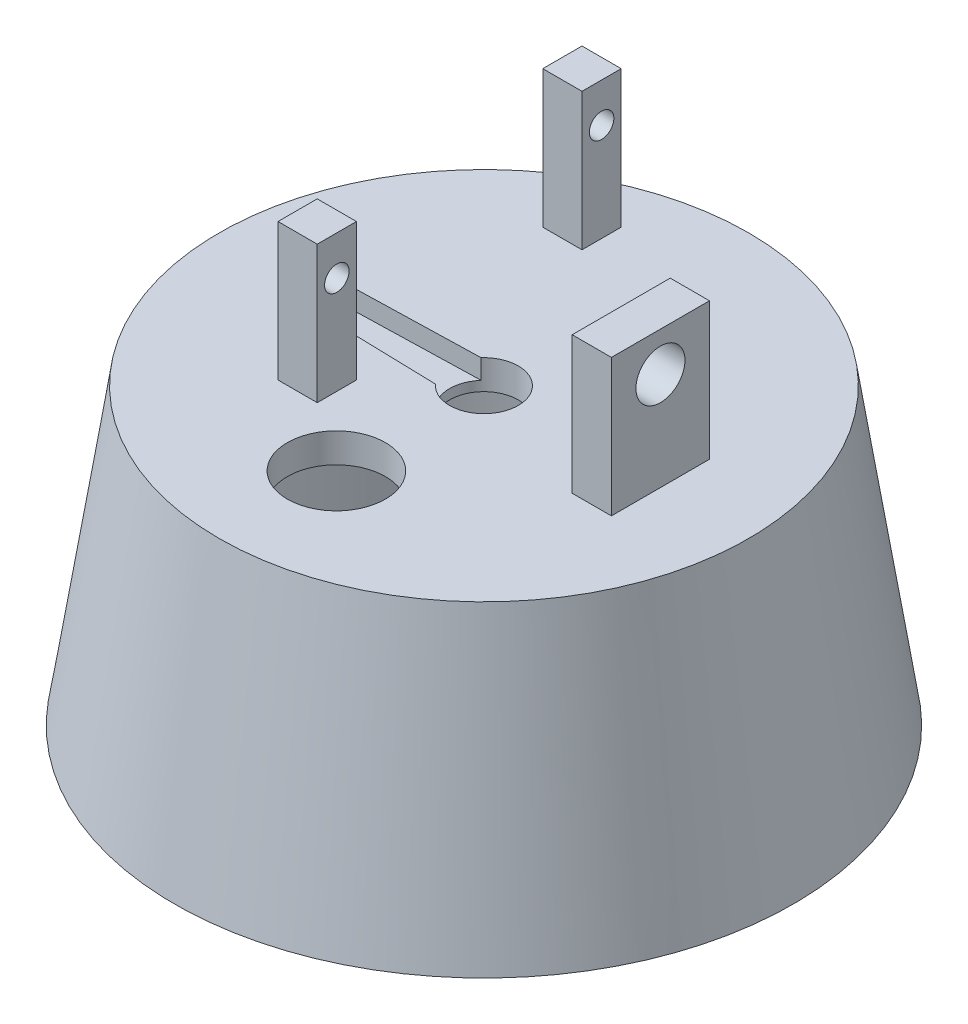
SolidWorks part; units mm, degrees
ref_plane "前视基准面" through (0, 0, 0) normal (0, 0, 1) x (1, 0, 0)
ref_plane "上视基准面" through (0, 0, 0) normal (0, 1, 0) x (1, 0, 0)
ref_plane "右视基准面" through (0, 0, 0) normal (1, 0, 0) x (0, 0, -1)
sketch "草图1" plane through (0, 0, 0) normal (0, 1, 0) x (1, 0, 0)
  circle A0 centre (0, 0) radius 27
  circle A1 centre (0, 0) radius 25.25
  dimension "D1" = 54
  dimension "D2" = 50.5
extrude "凸台-拉伸1" add sketch "草图1" along normal blind 27
sketch "草图3" plane through (0, 27, 0) normal (0, 1, 0) x (1, 0, 0)
  circle A0 centre (0, 0) radius 2.4
  circle A1 centre (0, 0) radius 27 construction
  circle A2 centre (0, 0) radius 27
  dimension "D1" = 4.8
extrude "凸台-拉伸2" add sketch "草图3" along normal blind 3
sketch "草图5" plane through (0, 0, 0) normal (0, 0, 1) x (1, 0, 0)
  line L0 (27, 30) -> (31.564, 0)
  line L1 (31.564, 0) -> (27, 0)
  line L2 (29.7, 0) -> (-29.7, 0) construction
  line L3 (27, 0) -> (27, 30) construction
  line L4 (27, 0) -> (27, 30)
  line L5 (0, 0) -> (0, 32.1264) construction
sketch "草图7" plane through (0, 30, 0) normal (0, 1, 0) x (1, 0, 0)
  line L0 (0, 5.5) -> (-29.1965, 5.5) construction
  line L2 (-7, 21) -> (-11, 21)
  line L3 (-7, 21) -> (-7, 17)
  line L4 (-7, 17) -> (-11, 17)
  line L5 (-11, 21) -> (-11, 17)
  line L6 (-11, -6) -> (-7, -6)
  line L7 (-11, -6) -> (-11, -10)
  line L8 (-11, -10) -> (-7, -10)
  line L9 (-7, -6) -> (-7, -10)
  dimension "D1" = 4
  dimension "D2" = 23
  dimension "D3" = 5.5
  dimension "D4" = 7
  dimension "D5" = 4
  dimension "D6" = 4
revolve "旋转2" add sketch "草图5" angle 360 about L5
extrude "凸台-拉伸3" add sketch "草图7" along normal blind 14
sketch "草图8" plane through (-7, 0, 0) normal (1, 0, 0) x (0, 0, -1)
  line L16 (-6, 40) -> (17, 40) construction
  line L17 (5.5, 40) -> (5.5, 30) construction
  line L18 (27, 30) -> (-27, 30) construction
  circle A0 centre (-8, 40) radius 1.25
  circle A1 centre (19, 40) radius 1.25
  point P0 (0, 0)
  dimension "D1" = 2.5
  dimension "D2" = 10
  dimension "D3" = 27
extrude "切除-拉伸1" cut sketch "草图8" against normal blind 14
sketch "草图10" plane through (0, 30, 0) normal (0, 1, 0) x (1, 0, 0)
  line L0 (0, 0) -> (-8.8896, 0) construction
  line L1 (14, -5) -> (18, -5)
  line L2 (14, -5) -> (14, 5)
  line L3 (14, 5) -> (18, 5)
  line L4 (18, -5) -> (18, 5)
  line L5 (16, 5) -> (16, -5) construction
  line L6 (14, 0) -> (18, 0) construction
  point P0 (16, 0)
  dimension "D1" = 18
  dimension "D2" = 4
  dimension "D3" = 10
extrude "凸台-拉伸4" add sketch "草图10" along normal blind 14
sketch "草图11" plane through (18, 0, 0) normal (1, 0, 0) x (0, 0, -1)
  line L0 (0, 44) -> (0, 30) construction
  line L1 (-5, 44) -> (5, 44) construction
  line L2 (27, 30) -> (-27, 30) construction
  circle A0 centre (-8, 40) radius 1.25 construction
  circle A2 centre (0, 40) radius 2.5
  point P15 (0, 0)
  point P16 (0, 0)
  dimension "D1" = 5
extrude "切除-拉伸3" cut sketch "草图11" against normal blind 14
sketch "草图12" plane through (0, 30, 0) normal (0, 1, 0) x (1, 0, 0)
  circle A0 centre (0, -15.0451) radius 5
extrude "切除-拉伸4" cut sketch "草图12" against normal blind 14
sketch "草图13" plane through (0, 30, 0) normal (0, 1, 0) x (1, 0, 0)
  line L0 (0, 0) -> (-23.4475, 0) construction
  line L1 (-15, 2) -> (-0.0641, 2.3991)
  line L2 (-15.0533, -1.9993) -> (-0.064, -2.3991)
  circle A0 centre (-15, 0) radius 2
  circle A1 centre (0, 0) radius 2.4 construction
  circle A2 centre (0, 0) radius 2.4
  circle A3 centre (0, 0) radius 3.5
  circle M6 centre (0, 0) radius 2.4
  dimension "D2" = 4
  dimension "D3" = 7
  dimension "D1" = 15
extrude "切除-拉伸5" cut sketch "草图13" against normal blind 2 contours L0 A3 L1 A0 | A3 L0 A0 L2 | L0 A2 L1 A3 | L0 A3 L2 M6 | A3 L0 A2 L2 | L0 A3 L1 M6
sketch "草图14" plane through (0, 28, 0) normal (0, 1, 0) x (1, 0, 0)
  line L2 (-15.0533, -1.9993) -> (-2.6106, -2.3312)
  line L3 (-2.6108, 2.3311) -> (-15, 2)
  line L4 (-15.0533, -1.9993) -> (-2.6106, -2.3312)
  line L5 (-2.6108, 2.3311) -> (-15, 2)
  circle A0 centre (0, 0) radius 3.5
  arc A2 (-2.6106, -2.3312) -> (-2.6108, 2.3311) centre (0, 0) ccw
  arc A3 (-15, 2) -> (-15.0533, -1.9993) centre (-15, 0) ccw
  arc A4 (-2.6106, -2.3312) -> (-2.6108, 2.3311) centre (0, 0) ccw
  arc A5 (-15, 2) -> (-15.0533, -1.9993) centre (-15, 0) ccw
  circle M9 centre (0, 0) radius 2.4
  arc M11 (-2.6106, -2.3312) -> (-2.6108, 2.3311) centre (0, 0) ccw
  dimension "D1" = 0
extrude "切除-拉伸6" cut sketch "草图14" against normal blind 91 contours A0 M11 M9
